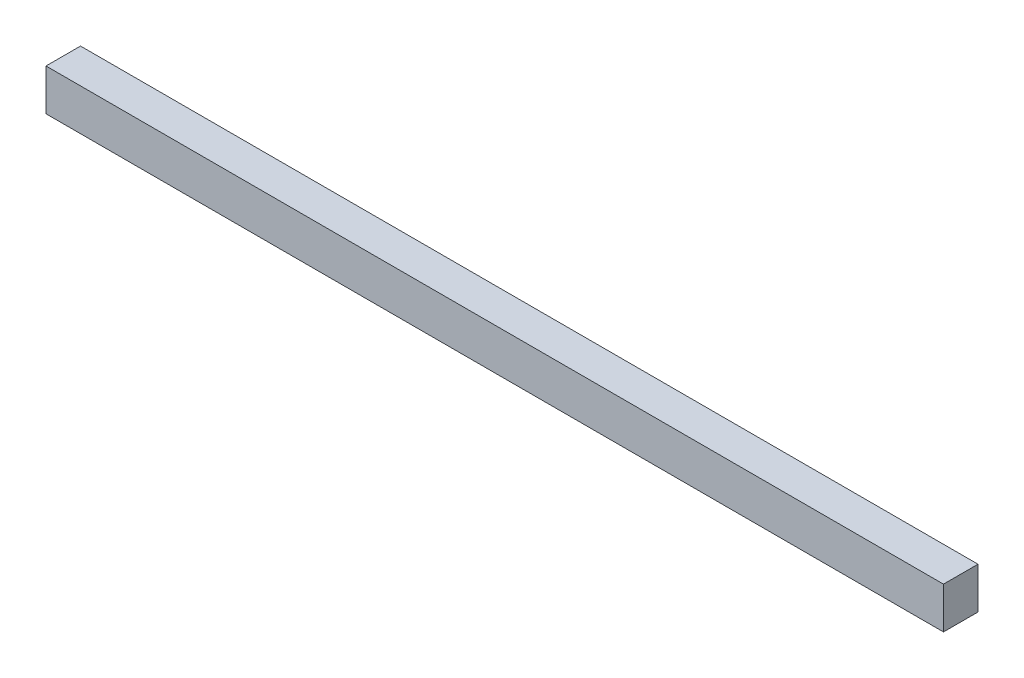
SolidWorks part; units mm, degrees
ref_plane "Front Plane" through (0, 0, 0) normal (0, 0, 1) x (1, 0, 0)
ref_plane "Top Plane" through (0, 0, 0) normal (0, 1, 0) x (1, 0, 0)
ref_plane "Right Plane" through (0, 0, 0) normal (1, 0, 0) x (0, 0, -1)
sketch "Sketch1" plane through (0, 0, 0) normal (0, 0, 1) x (1, 0, 0)
  line L1 (0, 0) -> (33.02, 0)
  line L2 (0, 0) -> (0, 1.524)
  line L3 (0, 1.524) -> (33.02, 1.524)
  line L4 (33.02, 0) -> (33.02, 1.524)
  dimension "D1" = 33.02
  dimension "D2" = 1.524
extrude "Boss-Extrude1" add sketch "Sketch1" along normal blind 1.27
